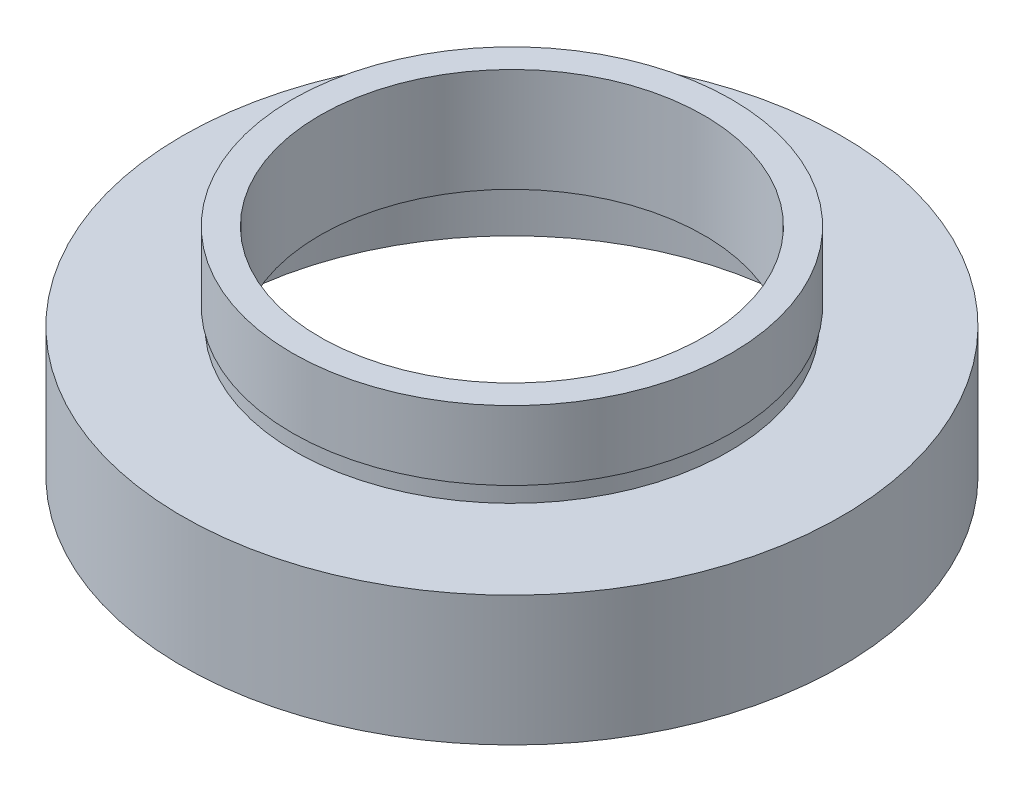
SolidWorks part; units mm, degrees
ref_plane "前视基准面" through (0, 0, 0) normal (0, 0, 1) x (1, 0, 0)
ref_plane "上视基准面" through (0, 0, 0) normal (0, 1, 0) x (1, 0, 0)
ref_plane "右视基准面" through (0, 0, 0) normal (1, 0, 0) x (0, 0, -1)
sketch "草图1" plane through (0, 0, 0) normal (0, 0, 1) x (1, 0, 0)
  line L0 (0, 16.886) -> (0, -24.4878) construction
  line L1 (17, 0) -> (17, 5.5)
  line L2 (11.1, 6.5) -> (17.6, 6.5)
  line L3 (11.1, 6.5) -> (11.1, 12.5)
  line L4 (11.1, 12.5) -> (12.7, 12.5)
  line L5 (12.7, 12.5) -> (12.7, 8.5)
  line L6 (12.7, 8.5) -> (12.55, 8.5)
  line L7 (12.55, 8.5) -> (12.55, 7.5)
  line L8 (12.55, 7.5) -> (19.05, 7.5)
  line L9 (19.05, 7.5) -> (19.05, 0)
  line L10 (19.05, 0) -> (17, 0)
  line L11 (17, 5.5) -> (17.6, 5.5)
  line L12 (17.6, 5.5) -> (17.6, 6.5)
  line L13 (0, 0) -> (3.4668, 0) construction
  point P4 (18.025, 0)
  dimension "D1" = 11.1
  dimension "D2" = 12.7
  dimension "D3" = 12.55
  dimension "D4" = 17
  dimension "D5" = 17.6
  dimension "D6" = 19.05
  dimension "D7" = 12.5
  dimension "D8" = 7.5
  dimension "D9" = 1
  dimension "D10" = 5.5
  dimension "D11" = 1
revolve "旋转1" add sketch "草图1" angle 360 about L0
cosmetic thread "装饰螺纹线1" parameters "D2"=24.4
cosmetic thread "装饰螺纹线2" parameters "D2"=23.2
cosmetic thread "装饰螺纹线3" parameters "D2"=35
